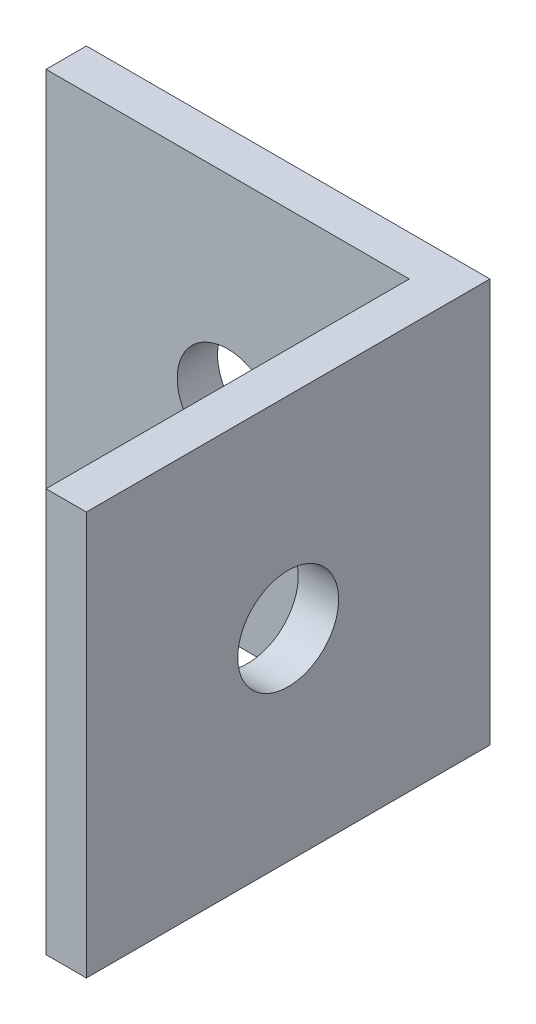
SolidWorks part; units mm, degrees
ref_plane "Front Plane" through (0, 0, 0) normal (0, 0, 1) x (1, 0, 0)
ref_plane "Top Plane" through (0, 0, 0) normal (0, 1, 0) x (1, 0, 0)
ref_plane "Right Plane" through (0, 0, 0) normal (1, 0, 0) x (0, 0, -1)
sketch "Sketch1" plane through (0, 0, 0) normal (0, 0, 1) x (1, 0, 0)
  line L1 (0, 0) -> (25.4, 0)
  line L2 (0, 0) -> (0, 25.4)
  line L3 (0, 25.4) -> (25.4, 25.4)
  line L4 (25.4, 0) -> (25.4, 25.4)
  dimension "D1" = 25.4
  dimension "D2" = 25.4
extrude "Boss-Extrude1" add sketch "Sketch1" along normal blind 2.54
sketch "Sketch2" plane through (25.4, 0, 0) normal (1, 0, 0) x (0, 0, -1)
  line L1 (0, 0) -> (-25.4, 0)
  line L2 (0, 0) -> (0, 25.4)
  line L3 (0, 25.4) -> (-25.4, 25.4)
  line L4 (-25.4, 0) -> (-25.4, 25.4)
  dimension "D1" = 25.4
  dimension "D2" = 25.4
extrude "Boss-Extrude2" add sketch "Sketch2" against normal blind 2.54
sketch "Sketch3" plane through (0, 0, 2.54) normal (0, 0, 1) x (1, 0, 0)
  line L0 (0, 25.4) -> (0, 0) construction
  line L1 (0, 0) -> (22.86, 0) construction
  circle A1 centre (11.43, 12.7) radius 3.175
  dimension "D2" = 6.35
  dimension "D4" = 11.43
  dimension "D5" = 12.7
extrude "Cut-Extrude1" cut sketch "Sketch3" against normal blind 2.54
sketch "Sketch4" plane through (22.86, 0, 0) normal (-1, 0, 0) x (0, 0, 1)
  line L0 (25.4, 25.4) -> (25.4, 0) construction
  line L1 (25.4, 0) -> (2.54, 0) construction
  circle A1 centre (12.7, 12.7) radius 3.175
  dimension "D2" = 6.35
  dimension "D3" = 12.7
  dimension "D4" = 12.7
extrude "Cut-Extrude2" cut sketch "Sketch4" against normal blind 2.54
